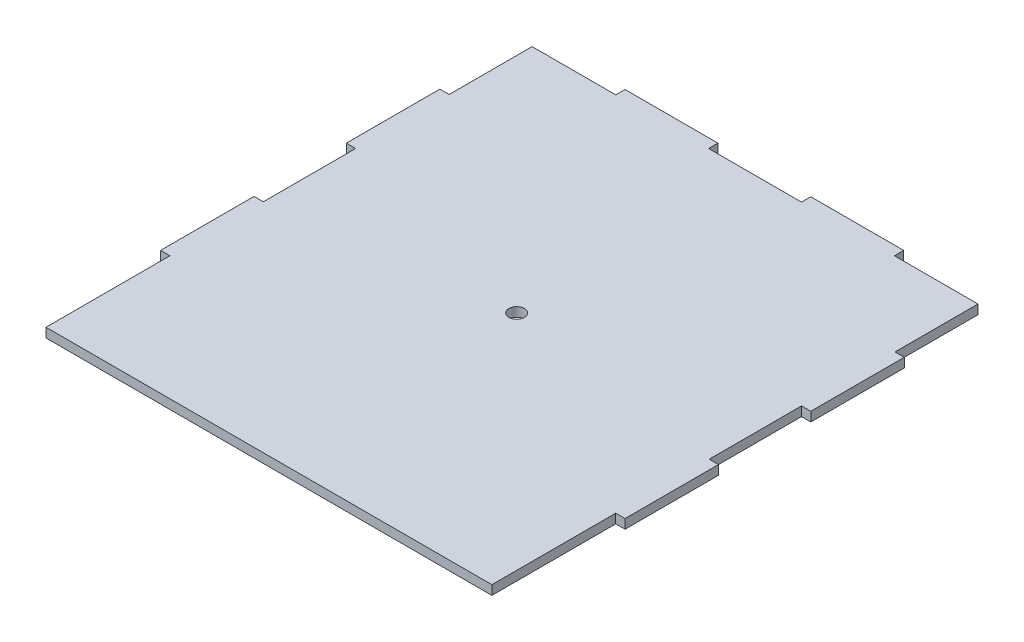
SolidWorks part; units mm, degrees
ref_plane "Front Plane" through (0, 0, 0) normal (0, 0, 1) x (1, 0, 0)
ref_plane "Top Plane" through (0, 0, 0) normal (0, 1, 0) x (1, 0, 0)
ref_plane "Right Plane" through (0, 0, 0) normal (1, 0, 0) x (0, 0, -1)
sketch "Sketch1" plane through (0, 0, 0) normal (0, 1, 0) x (1, 0, 0)
  line L0 (147, 130.2) -> (147, 160)
  line L1 (0, 0) -> (150, 0)
  line L2 (0, 0) -> (0, 160)
  line L3 (0, 160) -> (150, 160)
  line L4 (150, 0) -> (150, 160)
  line L5 (147, 0) -> (150, 0)
  line L6 (147, 0) -> (147, 40)
  line L7 (147, 40) -> (150, 40)
  line L8 (150, 0) -> (150, 40)
  line L9 (150, 70.2) -> (147, 70.2)
  line L10 (150, 70.2) -> (150, 100)
  line L11 (150, 100) -> (147, 100)
  line L12 (147, 70.2) -> (147, 100)
  line L13 (150, 130.2) -> (147, 130.2)
  line L17 (75, -840) -> (75, 49160) construction
  line L18 (3, 40) -> (0, 40)
  line L19 (0, 0) -> (0, 40)
  line L20 (3, 0) -> (0, 0)
  line L21 (3, 0) -> (3, 40)
  line L22 (0, 100) -> (3, 100)
  line L23 (3, 70.2) -> (3, 100)
  line L24 (0, 70.2) -> (3, 70.2)
  line L25 (0, 70.2) -> (0, 100)
  line L26 (0, 130.2) -> (3, 130.2)
  line L27 (3, 130.2) -> (3, 160)
  line L40 (90, 160) -> (90, 157)
  line L53 (150, 160) -> (120, 160)
  line L54 (150, 160) -> (150, 157)
  line L55 (150, 157) -> (120, 157)
  line L56 (120, 160) -> (120, 157)
  line L57 (90, 160) -> (60, 160)
  line L58 (60, 160) -> (60, 157)
  line L59 (90, 157) -> (60, 157)
  line L60 (30, 160) -> (30, 157)
  line L61 (30, 160) -> (0, 160)
  line L62 (0, 160) -> (0, 157)
  line L63 (30, 157) -> (0, 157)
  circle A0 centre (75, 80) radius 2.5
  point P21 (75, 160)
  dimension "D12" = 5
  dimension "D1" = 160
  dimension "D2" = 3
  dimension "D3" = 3
  dimension "D4" = 40
  dimension "D5" = 3
  dimension "D6" = 29.8
  dimension "D7" = 30.2
  dimension "D8" = 30.2
  dimension "D9" = 3
  dimension "D10" = 80
  dimension "D11" = 75
  dimension "D13" = 150
  dimension "D14" = 30
  dimension "D16" = 30
  dimension "D15" = 3
extrude "Boss-Extrude1" add sketch "Sketch1" along normal blind 3
